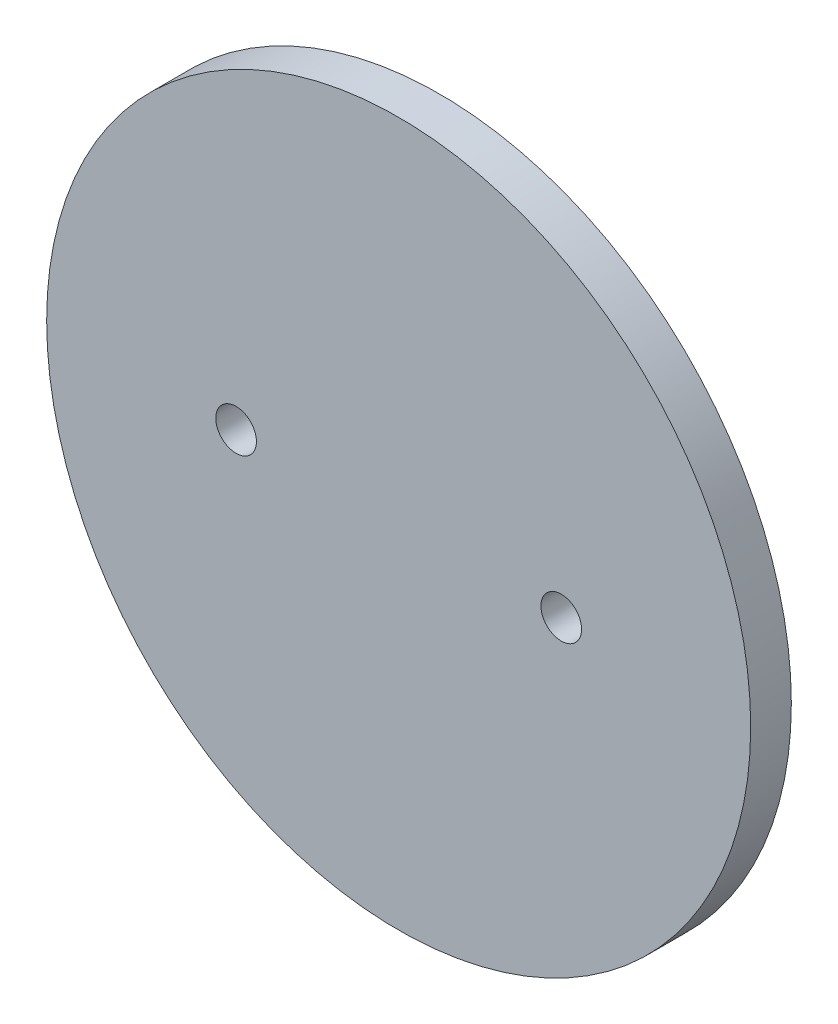
SolidWorks part; units mm, degrees
ref_plane "Front Plane" through (0, 0, 0) normal (0, 0, 1) x (1, 0, 0)
ref_plane "Top Plane" through (0, 0, 0) normal (0, 1, 0) x (1, 0, 0)
ref_plane "Right Plane" through (0, 0, 0) normal (1, 0, 0) x (0, 0, -1)
sketch "Sketch1" plane through (0, 0, 0) normal (0, 0, 1) x (1, 0, 0)
  circle A0 centre (0, 0) radius 22
extrude "Boss-Extrude1" add sketch "Sketch1" along normal blind 2.54
sketch "Sketch2" plane through (0, 0, 2.54) normal (0, 0, 1) x (1, 0, 0)
  line L0 (-22, 0) -> (22, 0)
  circle A0 centre (0, 0) radius 22 construction
  circle A1 centre (-10.16, 0) radius 1.27
  circle A2 centre (10.16, 0) radius 1.27
  point P7 (0, 0)
  dimension "D1" = 10.16
  dimension "D2" = 10.16
extrude "Cut-Extrude1" cut sketch "Sketch2" against normal through all contours L0 A1 | L0 A1 | L0 A2 | L0 A2
